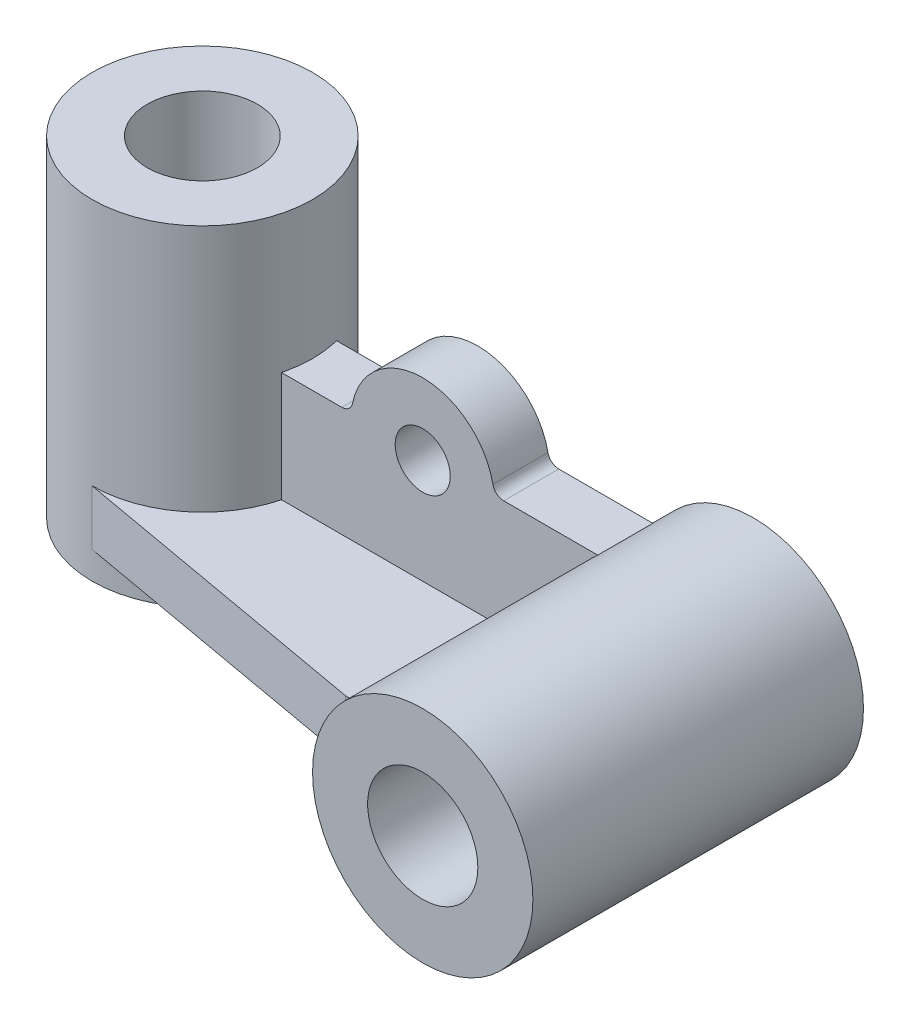
SolidWorks part; units mm, degrees
ref_plane "Front Plane" through (0, 0, 0) normal (0, 0, 1) x (1, 0, 0)
ref_plane "Top Plane" through (0, 0, 0) normal (0, 1, 0) x (1, 0, 0)
ref_plane "Right Plane" through (0, 0, 0) normal (1, 0, 0) x (0, 0, -1)
sketch "Sketch1" plane through (0, 0, 0) normal (0, 0, 1) x (1, 0, 0)
  line L0 (0, 26.3972) -> (0, -38.4527) construction
  line L1 (-53.3487, 0) -> (45.0346, 0) construction
  line L2 (0, 30) -> (0, -30)
  line L3 (0, -30) -> (20, -30)
  line L4 (20, -30) -> (20, 30)
  line L5 (20, 30) -> (0, 30)
  dimension "D1" = 60
  dimension "D2" = 20
revolve "cyl- purple" add sketch "Sketch1" angle 360 about L2
sketch "Sketch2" plane through (0, 30, 0) normal (0, 1, 0) x (1, 0, 0)
  circle A0 centre (0, 0) radius 10
  dimension "D1" = 20
extrude "Cut-Extrude1" cut sketch "Sketch2" against normal through all
ref_plane "Plane2" through (0, 0, 50) normal (0, 0, 1) x (1, 0, 0)
sketch "Sketch3" plane through (0, 0, 50) normal (0, 0, 1) x (1, 0, 0)
  line L0 (-41.145, 0) -> (181.0552, 0) construction
  line L1 (0, 53.1866) -> (0, -50.2505) construction
  line L2 (90, 47.9131) -> (90, -59.9766) construction
  line L3 (0, -30) -> (191.1627, -30) construction
  circle A0 centre (90, -10) radius 20
  circle A1 centre (90, -10) radius 10
  dimension "D1" = 40
  dimension "D2" = 20
  dimension "D3" = 90
  dimension "D4" = 30
  dimension "D5" = 20
extrude "cyl- blue" add sketch "Sketch3" against normal blind 60 separate body
ref_plane "Plane3" through (0, 0, -5) normal (0, 0, 1) x (1, 0, 0)
sketch "Sketch4" plane through (0, 0, -5) normal (0, 0, 1) x (1, 0, 0)
  line L0 (-19.6228, -30) -> (145.0037, -30) construction
  line L1 (-20, -30) -> (20, -30) construction
  line L2 (0, 39.5007) -> (0, -49.1941) construction
  line L4 (-38.69, -15) -> (133.7763, -15) construction
  line L5 (10, -15) -> (70.6351, -15)
  line L6 (10, 5) -> (30.3031, 5)
  line L8 (10, 5) -> (10, -15)
  line L9 (59.6969, 5) -> (76.7712, 5)
  circle A0 centre (90, -10) radius 20 construction
  arc A1 (70.6351, -15) -> (76.7712, 5) centre (90, -10) cw
  circle A4 centre (90, -10) radius 10 construction
  arc A7 (32.2627, 6.6) -> (57.7373, 6.6) centre (45, 4) cw
  circle A8 centre (45, 4) radius 5
  arc A9 (59.6969, 5) -> (57.7373, 6.6) centre (59.6969, 7) cw
  arc A10 (30.3031, 5) -> (32.2627, 6.6) centre (30.3031, 7) ccw
  dimension "D2" = 13
  dimension "D3" = 10
  dimension "D4" = 45
  dimension "D5" = 2
  dimension "D8" = 10
  dimension "D9" = 19
  dimension "D1" = 20
  dimension "D6" = 15
  dimension "D7" = 20
extrude "base- yellow" add sketch "Sketch4" along normal blind 10 separate body
ref_plane "Plane4" through (0, -25, 0) normal (0, 1, 0) x (1, 0, 0)
sketch "Sketch6" plane through (0, -25, 0) normal (0, 1, 0) x (1, 0, 0)
  line L0 (0, 35.6481) -> (0, 20) construction
  line L1 (-44.6641, 0) -> (126.7478, 0) construction
  line L8 (0, 0) -> (0, -43.6764) construction
  line L13 (110, -50) -> (110, -74.8178) construction
  line L14 (0, -20) -> (56, -30)
  line L17 (10, -5) -> (70.6351, -5) construction
  line L19 (19.3649, -5) -> (77.3091, -5)
  line L21 (56, -30) -> (77.3091, -30)
  line L22 (77.3091, -30) -> (77.3091, -5)
  circle A2 centre (0, 0) radius 20 construction
  arc A3 (0, -20) -> (19.3649, -5) centre (0, 0) ccw
  point P6 (70, -30)
  dimension "D1" = 25
  dimension "D2" = 56
  dimension "D3" = 14
  dimension "D4" = 77.3091
extrude "base-red" add sketch "Sketch6" along normal blind 10 separate body
